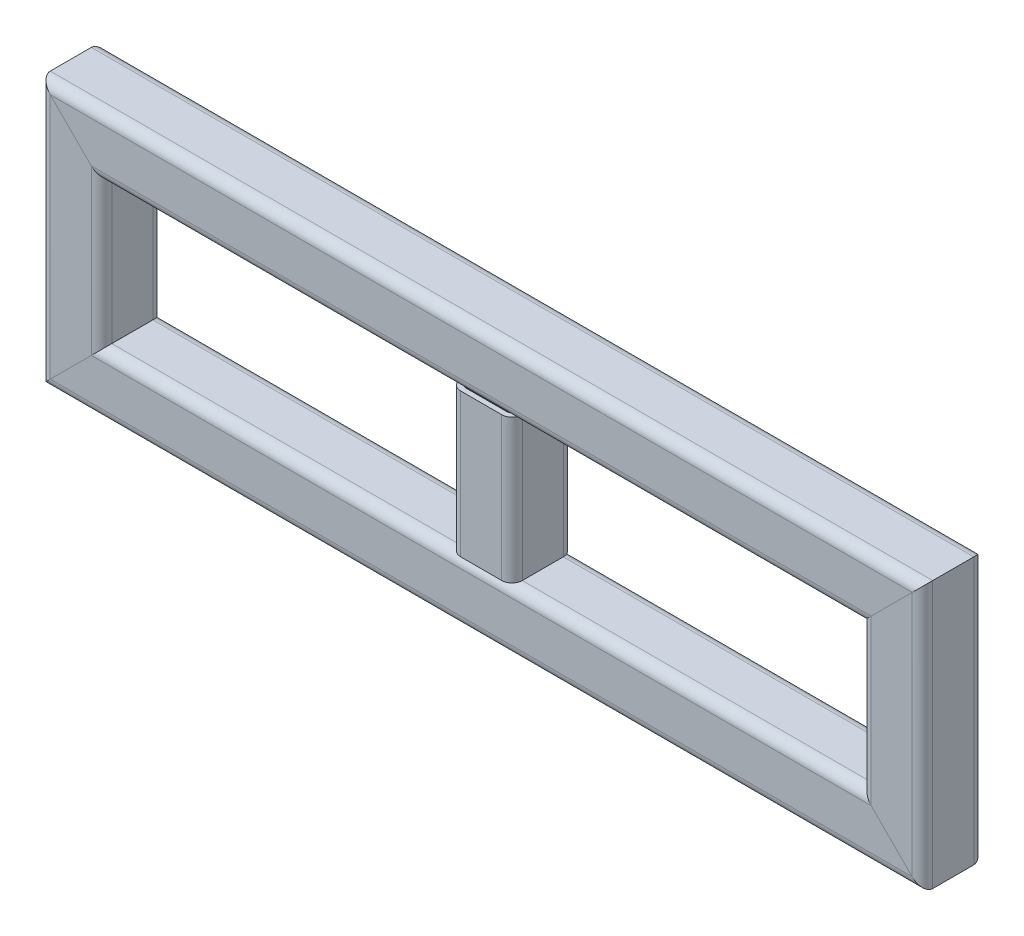
SolidWorks part; units mm, degrees
ref_plane "Front Plane" through (0, 0, 0) normal (0, 0, 1) x (1, 0, 0)
ref_plane "Top Plane" through (0, 0, 0) normal (0, 1, 0) x (1, 0, 0)
ref_plane "Right Plane" through (0, 0, 0) normal (1, 0, 0) x (0, 0, -1)
sketch3d "3DSketch1"
  line L0 (321.8482, 155.582, 0) -> (321.8482, 28.582, 0)
  line L1 (67.8482, 155.582, 0) -> (575.8482, 155.582, 0)
  line L2 (67.8482, 155.582, 0) -> (67.8482, 28.582, 0)
  line L3 (67.8482, 28.582, 0) -> (575.8482, 28.582, 0)
  line L4 (575.8482, 155.582, 0) -> (575.8482, 28.582, 0)
  dimension "D1" = 127
  dimension "D2" = 508
other "Structural Member1"
ref_plane "Plane1" through (67.8482, 155.582, 0) normal (0, -1, 0) x (1, 0, 0)
sketch "Sketch1" plane through (67.8482, 155.582, 0) normal (0, -1, 0) x (1, 0, 0)
  line L0 (-12.7, -15.875) -> (12.7, -15.875)
  line L1 (-15.875, -12.7) -> (-15.875, 12.7)
  line L2 (12.7, 15.875) -> (-12.7, 15.875)
  line L3 (15.875, 12.7) -> (15.875, -12.7)
  line L4 (-12.7, -19.05) -> (12.7, -19.05)
  line L5 (-19.05, -12.7) -> (-19.05, 12.7)
  line L6 (12.7, 19.05) -> (-12.7, 19.05)
  line L7 (19.05, 12.7) -> (19.05, -12.7)
  line L8 (-19.05, 0) -> (-15.875, 0) construction
  line L9 (-15.875, 0) -> (15.875, 0) construction
  line L10 (15.875, 0) -> (19.05, 0) construction
  line L11 (0, 19.05) -> (0, 15.875) construction
  line L12 (0, 15.875) -> (0, -15.875) construction
  line L13 (0, -15.875) -> (0, -19.05) construction
  arc A0 (19.05, 12.7) -> (12.7, 19.05) centre (12.7, 12.7) ccw
  arc A1 (12.7, -19.05) -> (19.05, -12.7) centre (12.7, -12.7) ccw
  arc A2 (-19.05, -12.7) -> (-12.7, -19.05) centre (-12.7, -12.7) ccw
  arc A3 (-12.7, 19.05) -> (-19.05, 12.7) centre (-12.7, 12.7) ccw
  arc A4 (-12.7, 15.875) -> (-15.875, 12.7) centre (-12.7, 12.7) ccw
  arc A5 (15.875, 12.7) -> (12.7, 15.875) centre (12.7, 12.7) ccw
  arc A6 (12.7, -15.875) -> (15.875, -12.7) centre (12.7, -12.7) ccw
  arc A7 (-15.875, -12.7) -> (-12.7, -15.875) centre (-12.7, -12.7) ccw
  point P6 (-19.05, -19.05)
  point P33 (-19.05, 19.05)
  point P35 (19.05, 19.05)
  point P36 (19.05, -19.05)
  point P37 (0, 0)
  dimension "D1" = 6.35
  dimension "Thickness" = 3.175
  dimension "V_leg" = 38.1
  dimension "H_leg" = 38.1
sketch "Sketch2" plane through (48.7982, 0, 0) normal (-1, 0, 0) x (0, 0, 1)
  line L0 (0, 174.632) -> (0, 9.532) construction
  line L1 (12.7, 174.632) -> (-12.7, 174.632) construction
  line L2 (-12.7, 9.532) -> (12.7, 9.532) construction
  line L3 (12.7, 92.082) -> (-12.7, 92.082) construction
  line L4 (12.7, 9.532) -> (12.7, 174.632) construction
  line L5 (-12.7, 9.532) -> (-12.7, 174.632) construction
sketch "Sketch3" plane through (594.8982, 0, 0) normal (1, 0, 0) x (0, 0, -1)
  line L0 (-12.7, 92.082) -> (12.7, 92.082) construction
  line L1 (-12.7, 174.632) -> (-12.7, 9.532) construction
  line L2 (12.7, 174.632) -> (12.7, 9.532) construction
  line L3 (0, 9.532) -> (0, 174.632) construction
  line L4 (-12.7, 9.532) -> (12.7, 9.532) construction
  line L5 (12.7, 174.632) -> (-12.7, 174.632) construction
sketch "Sketch4" plane through (0, 0, 19.05) normal (0, 0, 1) x (1, 0, 0)
  line L0 (588.5482, 92.082) -> (563.1482, 92.082) construction
  line L1 (588.5482, 168.282) -> (588.5482, 15.882) construction
  line L2 (563.1482, 142.882) -> (563.1482, 41.282) construction
  line L3 (575.8482, 28.582) -> (575.8482, 155.582) construction
  line L4 (588.5482, 15.882) -> (563.1482, 41.282) construction
  line L5 (563.1482, 142.882) -> (588.5482, 168.282) construction
